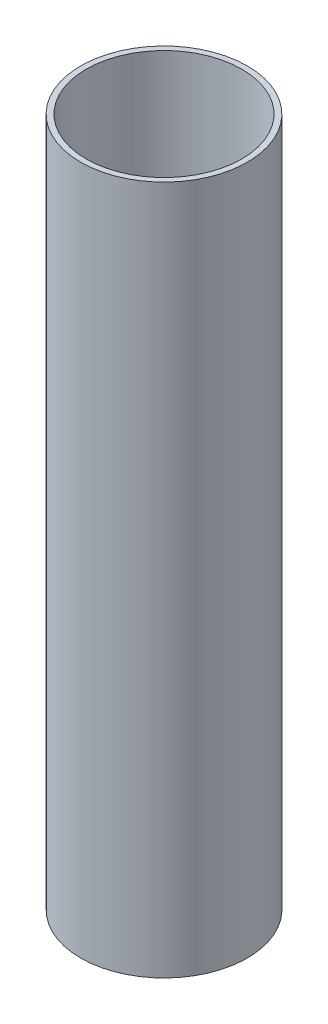
SolidWorks part; units mm, degrees
material "Fuzed Silica"
ref_plane "Front Plane" through (0, 0, 0) normal (0, 0, 1) x (1, 0, 0)
ref_plane "Top Plane" through (0, 0, 0) normal (0, 1, 0) x (1, 0, 0)
ref_plane "Right Plane" through (0, 0, 0) normal (1, 0, 0) x (0, 0, -1)
sketch "Sketch1" plane through (0, 0, 0) normal (0, 1, 0) x (1, 0, 0)
  circle A0 centre (0, 0) radius 35
  circle A1 centre (0, 0) radius 37.5
  dimension "D1" = 75
  dimension "D2" = 70
extrude "Boss-Extrude1" add sketch "Sketch1" along normal blind 310
